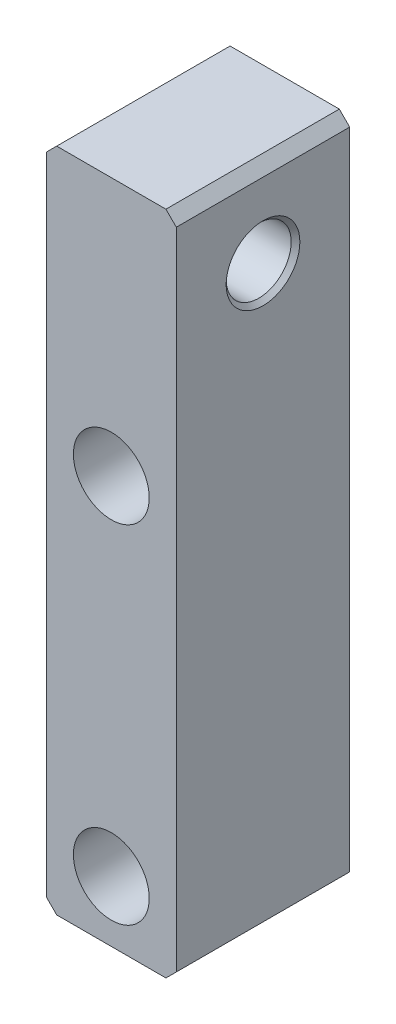
SolidWorks part; units mm, degrees
material "6061-T6 Al"
ref_plane "Front Plane" through (0, 0, 0) normal (0, 0, 1) x (1, 0, 0)
ref_plane "Top Plane" through (0, 0, 0) normal (0, 1, 0) x (1, 0, 0)
ref_plane "Right Plane" through (0, 0, 0) normal (1, 0, 0) x (0, 0, -1)
sketch "Sketch6" plane through (0, 0, 0) normal (0, 0, 1) x (1, 0, 0)
  line L2 (-8.001, 88.646) -> (8.001, 88.646)
  line L3 (-9.525, 87.122) -> (-9.525, -7.366)
  line L4 (-8.001, -8.89) -> (8.001, -8.89)
  line L5 (9.525, 87.122) -> (9.525, -7.366)
  line L6 (0, 88.646) -> (0, 0) construction
  line L13 (-9.525, 87.122) -> (-8.001, 88.646)
  line L14 (8.001, 88.646) -> (9.525, 87.122)
  line L15 (8.001, -8.89) -> (9.525, -7.366)
  line L16 (-9.525, -7.366) -> (-8.001, -8.89)
  dimension "D1" = 88.646
  dimension "D2" = 8.89
  dimension "D3" = 19.05
  dimension "D7" = 1.524
extrude "Boss-Extrude1" add sketch "Sketch6" against normal mid plane 25.4
hole_wizard "3/8-16 Tapped Hole1" positions "Sketch10" profile "Sketch11" tap size "3/8-16" standard "ANSI Inch" end condition through all
sketch "Sketch10" plane through (9.525, -2.3947, -10.3524) normal (-1, 0, 0) x (0, 0, 1)
  line L0 (20.8299, 2.3947) -> (-0.1251, 2.3947) construction
  point P0 (10.3524, 78.5947)
  dimension "D1" = 76.2
sketch "Sketch11" plane through (9.525, 76.2, 0) normal (0, 1, 0) x (0, 0, -1)
  line L0 (0, 0) -> (0, 19.05)
  line L1 (0, 19.05) -> (5.3975, 19.05)
  line L2 (4.7625, 18.415) -> (4.7625, 0.635)
  line L3 (4.7625, 0.635) -> (5.3975, 0)
  line L5 (5.3975, 0) -> (0, 0)
  line L6 (-4.7625, 0.635) -> (-5.3975, 0) construction
  line L7 (5.3975, 19.05) -> (4.7625, 18.415)
  line L8 (-5.3975, 19.05) -> (-4.7625, 18.415) construction
  line L11 (0, -6.35) -> (0, 107.95) construction
  dimension "Thread Major Dia." = 9.525
  dimension "Thru Tap Drill Depth" = 19.05
  dimension "Near C'Sink Dia." = 10.795
  dimension "Near C'Sink Angle" = 90
  dimension "Far C'Sink Dia." = 10.795
  dimension "Far C'Sink Angle" = 90
hole_wizard "CBORE for 1/4 Socket Head Cap Screw1" positions "Sketch13" profile "Sketch12" counterbore size "1/4" standard "ANSI Inch" end condition up to next
sketch "Sketch13" plane through (0, 0, 12.7) normal (0, 0, 1) x (1, 0, 0)
  line L0 (0, 88.646) -> (0, 0) construction
  point P0 (0, 0)
  point P3 (0, 50.8)
  dimension "D1" = 50.8
sketch "Sketch12" plane through (0, 0, 12.7) normal (1, 0, 0) x (0, -1, 0)
  line L0 (0, 0) -> (0, 25.4)
  line L1 (0, 25.4) -> (3.3782, 25.4)
  line L3 (3.3782, 25.4) -> (3.3782, 9.652)
  line L4 (3.3782, 9.652) -> (5.5562, 9.652)
  line L5 (5.5562, 9.652) -> (5.5562, 0)
  line L7 (5.5562, 0) -> (0, 0)
  line L11 (0, -6.35) -> (0, 107.95) construction
  dimension "Thru Hole Dia." = 6.7564
  dimension "Thru Hole Depth" = 25.4
  dimension "C'Bore Dia." = 11.1125
  dimension "C'Bore Depth" = 9.652
